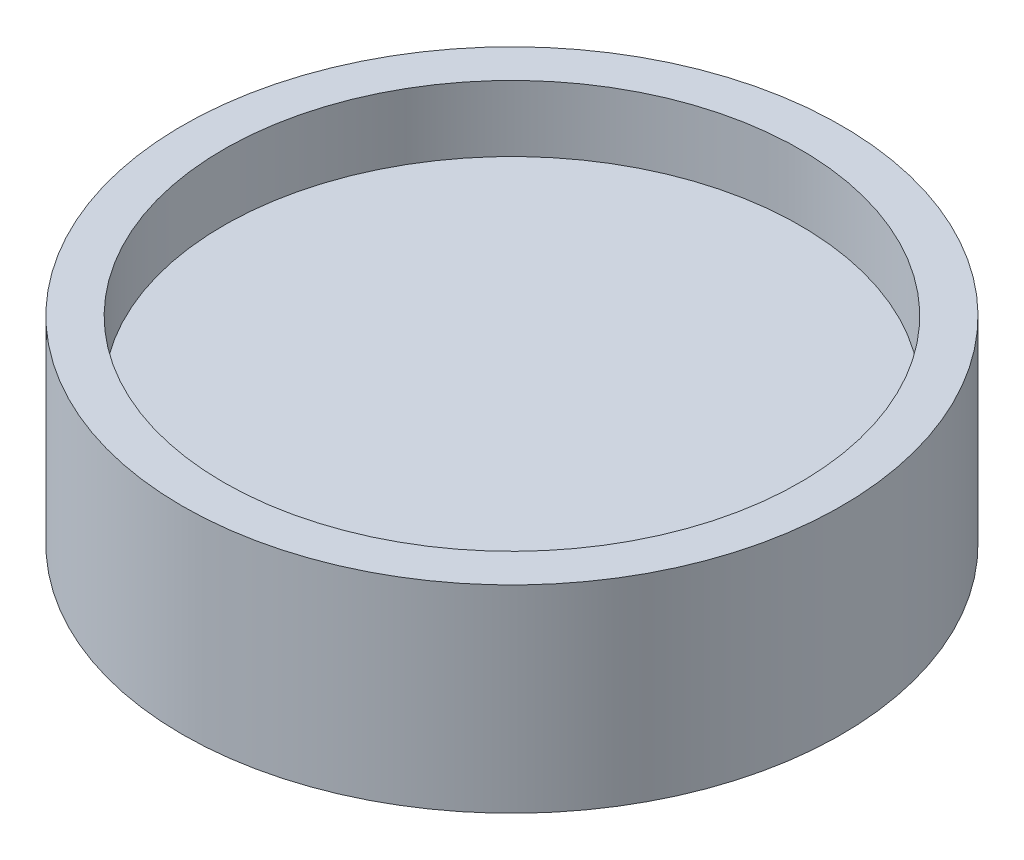
SolidWorks part; units mm, degrees
ref_plane "Plan de face" through (0, 0, 0) normal (0, 0, 1) x (1, 0, 0)
ref_plane "Plan de dessus" through (0, 0, 0) normal (0, 1, 0) x (1, 0, 0)
ref_plane "Plan de droite" through (0, 0, 0) normal (1, 0, 0) x (0, 0, -1)
sketch "Esquisse1" plane through (0, 0, 0) normal (0, 1, 0) x (1, 0, 0)
  circle A0 centre (0, 0) radius 40
  dimension "D1" = 80
extrude "Boss.-Extru.1" add sketch "Esquisse1" along normal blind 24
sketch "Esquisse2" plane through (0, 24, 0) normal (0, 1, 0) x (1, 0, 0)
  circle A0 centre (0, 0) radius 35
  dimension "D1" = 70
extrude "Enlèv. mat.-Extru.1" cut sketch "Esquisse2" against normal blind 8
sketch "Esquisse3" plane through (0, 0, 0) normal (0, -1, 0) x (1, 0, 0)
  circle A0 centre (0, 0) radius 35
  dimension "D1" = 70
extrude "Enlèv. mat.-Extru.2" cut sketch "Esquisse3" against normal blind 8
